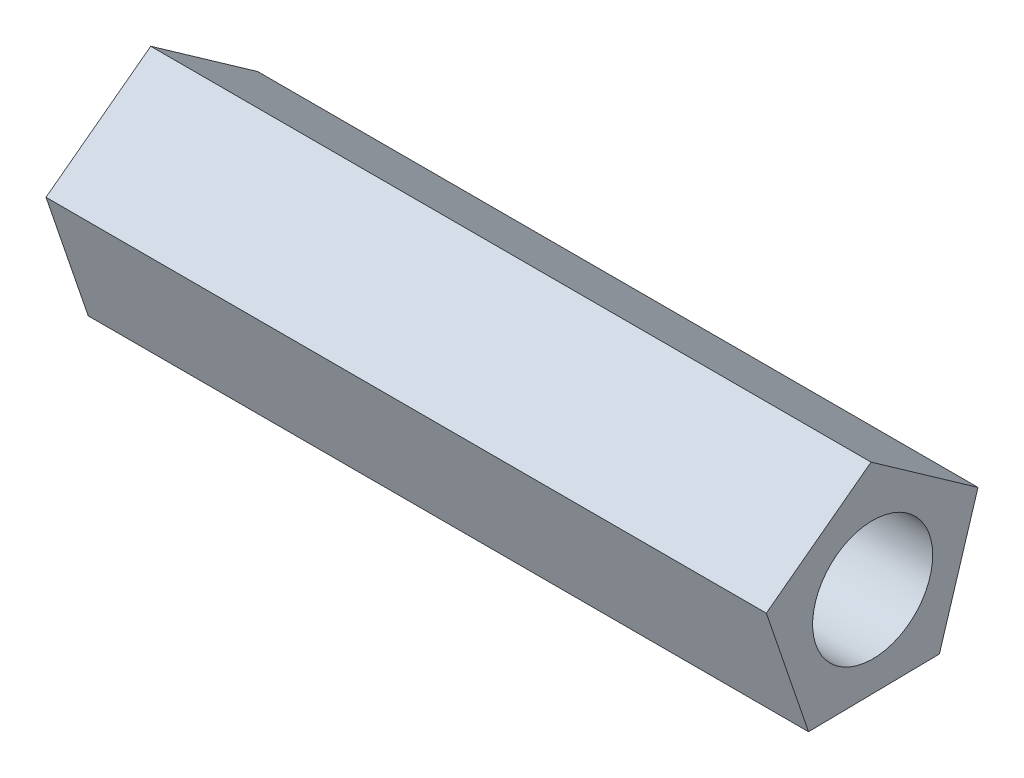
SolidWorks part; units mm, degrees
material "6063-O"
ref_plane "Front Plane" through (0, 0, 0) normal (0, 0, 1) x (1, 0, 0)
ref_plane "Top Plane" through (0, 0, 0) normal (0, 1, 0) x (1, 0, 0)
ref_plane "Right Plane" through (0, 0, 0) normal (1, 0, 0) x (0, 0, -1)
sketch "Sketch6" plane through (0, 0, 0) normal (1, 0, 0) x (0, 0, -1)
  line L1 (5.5571, -7.4203) -> (8.7744, 2.9921)
  line L2 (8.7744, 2.9921) -> (-0.1343, 9.2695)
  line L3 (-0.1343, 9.2695) -> (-8.8573, 2.7368)
  line L4 (-8.8573, 2.7368) -> (-5.3399, -7.5781)
  line L5 (-5.3399, -7.5781) -> (5.5571, -7.4203)
  circle A0 centre (0, 0) radius 7.5 construction
  circle A1 centre (0, 0) radius 5
  dimension "D1" = 15
  dimension "D2" = 10
extrude "Boss-Extrude2" add sketch "Sketch6" along normal mid plane 60
